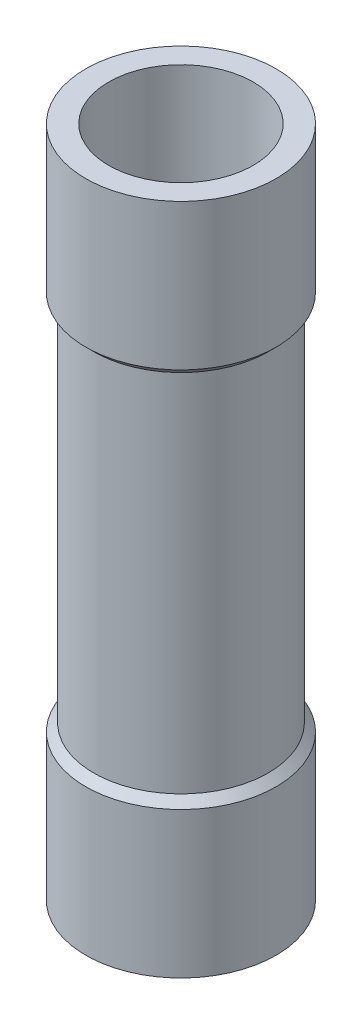
SolidWorks part; units mm, degrees
ref_plane "Front Plane" through (0, 0, 0) normal (0, 0, 1) x (1, 0, 0)
ref_plane "Top Plane" through (0, 0, 0) normal (0, 1, 0) x (1, 0, 0)
ref_plane "Right Plane" through (0, 0, 0) normal (1, 0, 0) x (0, 0, -1)
sketch "Sketch1" plane through (0, 0, 0) normal (0, 0, 1) x (1, 0, 0)
  line L0 (0, 0) -> (0, 50000) construction
  line L1 (2.894, 13.462) -> (2.894, -13.462)
  line L2 (1.5875, -7.62) -> (2.794, -7.62)
  line L3 (1.5875, -7.62) -> (1.5875, 7.62)
  line L4 (1.5875, 7.62) -> (2.794, 7.62)
  line L5 (2.794, -7.62) -> (2.794, 7.62)
  line L6 (1.5875, -7.62) -> (2.794, 7.62) construction
  line L7 (1.5875, 7.62) -> (2.794, -7.62) construction
  line L8 (2.894, -13.462) -> (3.81, -13.462)
  line L9 (3.81, -13.462) -> (3.81, -7.62)
  line L10 (3.81, -7.62) -> (3.4925, -7.3025)
  line L11 (3.4925, -7.3025) -> (3.4925, 7.3025)
  line L12 (3.4925, 7.3025) -> (3.81, 7.62)
  line L13 (3.81, 7.62) -> (3.81, 13.462)
  line L14 (3.81, 13.462) -> (2.894, 13.462)
  line L15 (3.4925, 0) -> (0, 0) construction
  point P3 (2.1907, 0)
  dimension "D1" = 3.175
  dimension "D2" = 5.588
  dimension "D3" = 15.24
  dimension "D4" = 0.1
  dimension "D5" = 6.985
  dimension "D6" = 7.62
  dimension "D7" = 26.924
revolve "Revolve1" add sketch "Sketch1" angle 360 about L0
